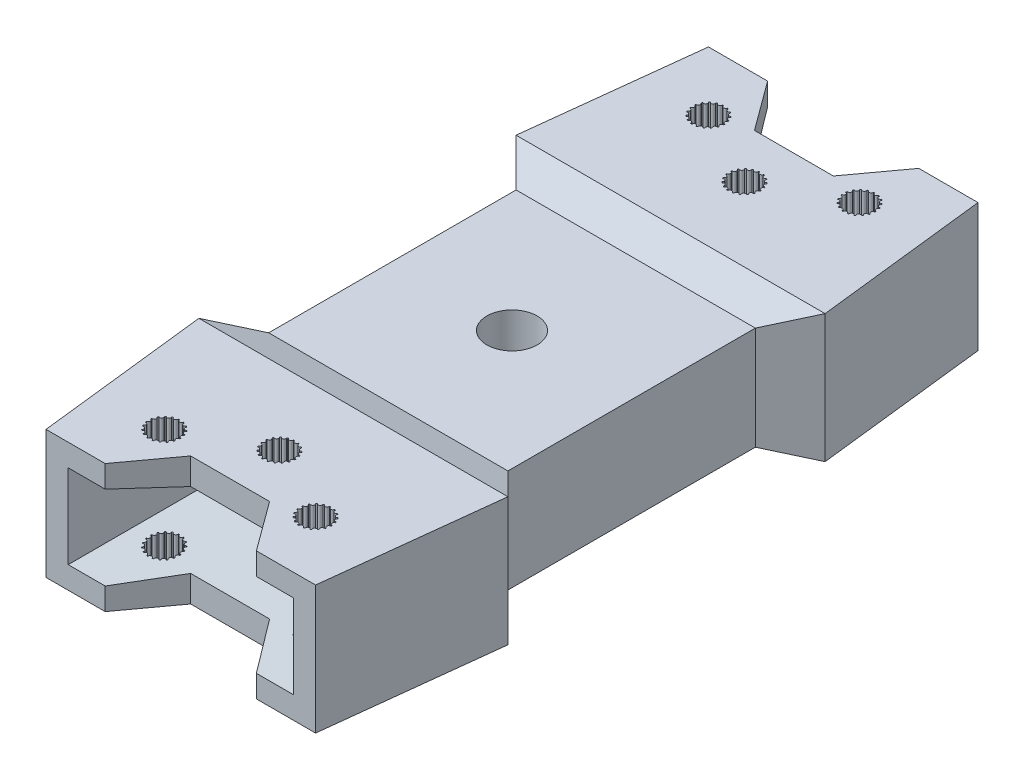
SolidWorks part; units mm, degrees
material "ABS"
ref_plane "Front Plane" through (0, 0, 0) normal (0, 0, 1) x (1, 0, 0)
ref_plane "Top Plane" through (0, 0, 0) normal (0, 1, 0) x (1, 0, 0)
ref_plane "Right Plane" through (0, 0, 0) normal (1, 0, 0) x (0, 0, -1)
sketch "Sketch2" plane through (0, 0, 0) normal (0, 1, 0) x (1, 0, 0)
  line L0 (0, 0) -> (0, 3) construction
  line L1 (0, 175) -> (168.3275, 175) construction
  line L2 (168.3275, 175) -> (-205.8504, 175) construction
  line L3 (-15, 350) -> (-35, 175)
  line L4 (-35, 175) -> (-15, 0)
  line L5 (15, 350) -> (35, 175)
  line L6 (35, 175) -> (15, 0)
  line L7 (0, 335) -> (0, 350) construction
  line L8 (31.3255, 207.1517) -> (24.2545, 200.0806)
  line L9 (24.2545, 200.0806) -> (24.2545, 149.9194)
  line L10 (31.3255, 142.8483) -> (24.2545, 149.9194)
  line L11 (-31.3255, 142.8483) -> (-24.2545, 149.9194)
  line L12 (-24.2545, 200.0806) -> (-24.2545, 149.9194)
  line L13 (-31.3255, 207.1517) -> (-24.2545, 200.0806)
  circle A0 centre (0, 350) radius 3
  circle A1 centre (0, 0) radius 3
  arc A2 (15, 350) -> (-15, 350) centre (0, 350) ccw
  arc A3 (-15, 0) -> (15, 0) centre (0, 0) ccw
  circle A4 centre (0, 175) radius 5.1
  point P21 (24.2545, 175)
  dimension "D2" = 6
  dimension "D3" = 6
  dimension "D4" = 30
  dimension "D5" = 30
  dimension "D7" = 10.2
  dimension "D1" = 350
  dimension "D6" = 35
  dimension "D8" = 32.1517
  dimension "D9" = 10
extrude "Boss-Extrude1" add sketch "Sketch2" along normal blind 26 contours L4 A3 L6 L10 L9 L8 L5 A2 L3 L13 L12 L11 A4 A0 A1
sketch "Sketch3" plane through (0, 0, 0) normal (1, 0, 0) x (0, 0, -1)
  line L0 (-15, 13) -> (370.2756, 13) construction
  line L1 (-15, 26) -> (-15, 0) construction
  line L3 (177.6378, 13) -> (177.6378, -89.1144) construction
  line L5 (-50, 21) -> (20, 21)
  line L6 (-50, 21) -> (-50, 5)
  line L7 (-50, 5) -> (20, 5)
  line L8 (20, 21) -> (20, 5)
  line L9 (-50, 21) -> (20, 5) construction
  line L10 (-50, 5) -> (20, 21) construction
  dimension "D1" = 16
  dimension "D2" = 35
extrude "Cut-Extrude1" cut sketch "Sketch3" against normal mid plane 55
sketch "Sketch4" plane through (0, 26, 0) normal (0, 1, 0) x (1, 0, 0)
  circle A0 centre (0, 175) radius 5
sketch "Sketch5" plane through (24.2545, 0, 0) normal (1, 0, 0) x (0, 0, -1)
  line L0 (149.9194, 13) -> (220.8721, 13) construction
  line L1 (149.9194, 26) -> (149.9194, 0) construction
  line L2 (175, 0) -> (175, 36.8039) construction
  line L3 (200.0806, 0) -> (149.9194, 0) construction
  line L4 (142.8483, 26) -> (149.9194, 23.4568)
  line L5 (149.9194, 23.4568) -> (200.0806, 23.4568)
  line L6 (142.8483, 26) -> (207.1517, 26)
  line L7 (207.1517, 26) -> (200.0806, 23.4568)
  line L8 (207.1517, 0) -> (200.0806, 2.5432)
  line L9 (149.9194, 2.5432) -> (200.0806, 2.5432)
  line L10 (142.8483, 0) -> (149.9194, 2.5432)
  line L11 (142.8483, 0) -> (207.1517, 0)
  point P14 (175, 23.4568)
  point P15 (175, 26)
extrude "Cut-Extrude2" cut sketch "Sketch5" against normal mid plane 126
ref_plane "Plane1" through (0, 0, -175) normal (0, 0, 1) x (1, 0, 0)
mirror "Mirror3" about plane through (0, 0, -175) normal (0, 0, 1) of "Cut-Extrude1"
sketch "Sketch9" plane through (0, 23.4568, 0) normal (0, 1, 0) x (1, 0, 0)
  line L0 (-27.3255, 107.8483) -> (-15.3255, 107.8483)
  line L1 (-31.3255, 142.8483) -> (-15, 0) construction
  line L2 (-15.3255, 107.8483) -> (-8, 117.8483)
  line L3 (-8, 117.8483) -> (8, 117.8483)
  line L4 (0, 175) -> (0, 30.7184) construction
  line L5 (-27.3255, 107.8483) -> (-31.0297, 97.9185)
  line L6 (-31.0297, 97.9185) -> (-17.7384, -19.4473)
  line L7 (-17.7384, -19.4473) -> (15.9415, -24.7304)
  line L8 (15.9415, -24.7304) -> (32.6609, 107.8483)
  line L9 (32.6609, 107.8483) -> (27.3255, 107.8483)
  line L10 (31.3255, 142.8483) -> (15, 0) construction
  line L11 (15.3255, 107.8483) -> (8, 117.8483)
  line L12 (27.3255, 107.8483) -> (15.3255, 107.8483)
  line L13 (-31.3255, 142.8483) -> (31.3255, 142.8483) construction
  line L14 (-15.3255, 107.8483) -> (-15.3255, 124.8534) construction
  line L23 (-31.3255, 142.8483) -> (44.7301, 142.8483) construction
  circle A0 centre (0, 127.8483) radius 2
  circle A1 centre (-15.3255, 119.8483) radius 2
  circle A2 centre (15.3255, 119.8483) radius 2
  point P18 (0, 117.8483)
  point P40 (0.5017, 119.3533)
  dimension "D4" = 4
  dimension "D6" = 4
  dimension "D1" = 25
  dimension "D2" = 16
  dimension "D3" = 12
  dimension "D5" = 10
  dimension "D7" = 12
  dimension "D8" = 12
  dimension "D9" = 10
extrude "Cut-Extrude3" cut sketch "Sketch9" along normal blind 68 and the other way blind 68
sketch "Sketch10" plane through (0, 0, -107.8483) normal (0, 0, 1) x (1, 0, 0)
  line L0 (-22.8255, 4.5) -> (22.8255, 4.5)
  line L5 (22.8255, 4.5) -> (22.8255, 21.5)
  line L6 (-22.8255, 21.5) -> (22.8255, 21.5)
  line L7 (-22.8255, 4.5) -> (-22.8255, 21.5)
  line L8 (-27.3255, 0) -> (-27.3255, 26) construction
  line L10 (27.3255, 0) -> (27.3255, 26) construction
  line L11 (8, 26) -> (-8, 26) construction
  line L12 (8, 0) -> (-8, 0) construction
  line M9 (-15.3255, 0) -> (-15.3255, 26)
  dimension "D1" = 4.5
  dimension "D2" = 4.5
  dimension "D3" = 4.5
  dimension "D4" = 4.5
extrude "Cut-Extrude4" cut sketch "Sketch10" against normal blind 28 draft 5 contours L6 L0 L5 M9 | L7 L0 L6 M9
mirror "Mirror5" about plane through (0, 0, -175) normal (0, 0, 1) of "Cut-Extrude4", "Cut-Extrude3"
sketch "Sketch11" plane through (0, 0, 0) normal (0, -1, 0) x (1, 0, 0)
  line L0 (0, -117.8483) -> (0, -161.1562) construction
  line L1 (8, -117.8483) -> (-8, -117.8483) construction
  line L2 (-15.3255, -119.8483) -> (-22.194, -119.8483) construction
  circle A0 centre (-15.3255, -119.8483) radius 3.25
  circle A1 centre (-18.5755, -119.8483) radius 0.4
  circle A2 centre (-18.3994, -118.793) radius 0.4
  circle A3 centre (-17.8902, -117.8521) radius 0.4
  circle A4 centre (-17.1031, -117.1275) radius 0.4
  circle A5 centre (-16.1233, -116.6977) radius 0.4
  circle A6 centre (-15.0571, -116.6094) radius 0.4
  circle A7 centre (-14.02, -116.872) radius 0.4
  circle A8 centre (-13.1244, -117.4572) radius 0.4
  circle A9 centre (-12.4672, -118.3015) radius 0.4
  circle A10 centre (-12.1198, -119.3134) radius 0.4
  circle A11 centre (-12.1198, -120.3832) radius 0.4
  circle A12 centre (-12.4672, -121.3951) radius 0.4
  circle A13 centre (-13.1244, -122.2394) radius 0.4
  circle A14 centre (-14.02, -122.8246) radius 0.4
  circle A15 centre (-15.0571, -123.0872) radius 0.4
  circle A16 centre (-16.1233, -122.9988) radius 0.4
  circle A17 centre (-17.1031, -122.5691) radius 0.4
  circle A18 centre (-17.8902, -121.8445) radius 0.4
  circle A19 centre (-18.3994, -120.9036) radius 0.4
  circle A20 centre (0, -127.8483) radius 3.25
  circle A21 centre (15.3255, -119.8483) radius 3.25
  circle A22 centre (-3.25, -127.8483) radius 0.4
  circle A23 centre (12.0755, -119.8483) radius 0.4
  circle A24 centre (-3.0739, -126.793) radius 0.4
  circle A25 centre (-2.5647, -125.8521) radius 0.4
  circle A26 centre (-1.7776, -125.1275) radius 0.4
  circle A27 centre (-0.7978, -124.6977) radius 0.4
  circle A28 centre (0.2684, -124.6094) radius 0.4
  circle A29 centre (1.3055, -124.872) radius 0.4
  circle A30 centre (2.2012, -125.4572) radius 0.4
  circle A31 centre (2.8583, -126.3015) radius 0.4
  circle A32 centre (3.2057, -127.3134) radius 0.4
  circle A33 centre (3.2057, -128.3832) radius 0.4
  circle A34 centre (2.8583, -129.3951) radius 0.4
  circle A35 centre (2.2012, -130.2394) radius 0.4
  circle A36 centre (1.3055, -130.8246) radius 0.4
  circle A37 centre (0.2684, -131.0872) radius 0.4
  circle A38 centre (-0.7978, -130.9988) radius 0.4
  circle A39 centre (-1.7776, -130.5691) radius 0.4
  circle A40 centre (-2.5647, -129.8445) radius 0.4
  circle A41 centre (-3.0739, -128.9036) radius 0.4
  circle A42 centre (12.2516, -118.793) radius 0.4
  circle A43 centre (12.7608, -117.8521) radius 0.4
  circle A44 centre (13.5479, -117.1275) radius 0.4
  circle A45 centre (14.5277, -116.6977) radius 0.4
  circle A46 centre (15.5939, -116.6094) radius 0.4
  circle A47 centre (16.631, -116.872) radius 0.4
  circle A48 centre (17.5267, -117.4572) radius 0.4
  circle A49 centre (18.1838, -118.3015) radius 0.4
  circle A50 centre (18.5312, -119.3134) radius 0.4
  circle A51 centre (18.5312, -120.3832) radius 0.4
  circle A52 centre (18.1838, -121.3951) radius 0.4
  circle A53 centre (17.5267, -122.2394) radius 0.4
  circle A54 centre (16.631, -122.8246) radius 0.4
  circle A55 centre (15.5939, -123.0872) radius 0.4
  circle A56 centre (14.5277, -122.9988) radius 0.4
  circle A57 centre (13.5479, -122.5691) radius 0.4
  circle A58 centre (12.7608, -121.8445) radius 0.4
  circle A59 centre (12.2516, -120.9036) radius 0.4
  circle M2 centre (15.3255, -119.8483) radius 2
  circle M3 centre (-15.3255, -119.8483) radius 2
  circle M4 centre (0, -127.8483) radius 2
  dimension "D1" = 6.5
  dimension "D2" = 0.8
  dimension "D4" = 6.5
  dimension "D5" = 6.5
  dimension "D6" = 0.8
  dimension "D7" = 0.8
  dimension "D3" = 19
  dimension "D8" = 19
  dimension "D9" = 19
extrude "Cut-Extrude5" cut sketch "Sketch11" against normal blind 54 contours A19 A0 A18 A17 A16 A15 A14 A13 A12 A11 A10 A9 A8 A7 A6 A5 A4 A3 A2 A1 M3 | A41 A20 A40 A39 A38 A37 A36 A35 A34 A33 A32 A31 A30 A29 A28 A27 A26 A25 A24 A22 M4 | A59 A21 A58 A57 A56 A55 A54 A53 A52 A51 A50 A49 A48 A47 A46 A45 A44 A43 A42 A23 M2
mirror "Mirror6" about plane through (0, 0, -175) normal (0, 0, 1) of "Cut-Extrude5"
sketch "Sketch12" plane through (0, 2.5432, 0) normal (0, -1, 0) x (1, 0, 0)
  circle A0 centre (0, -175) radius 8.5
  dimension "D1" = 17
extrude "Cut-Extrude6" cut sketch "Sketch12" against normal blind 10
